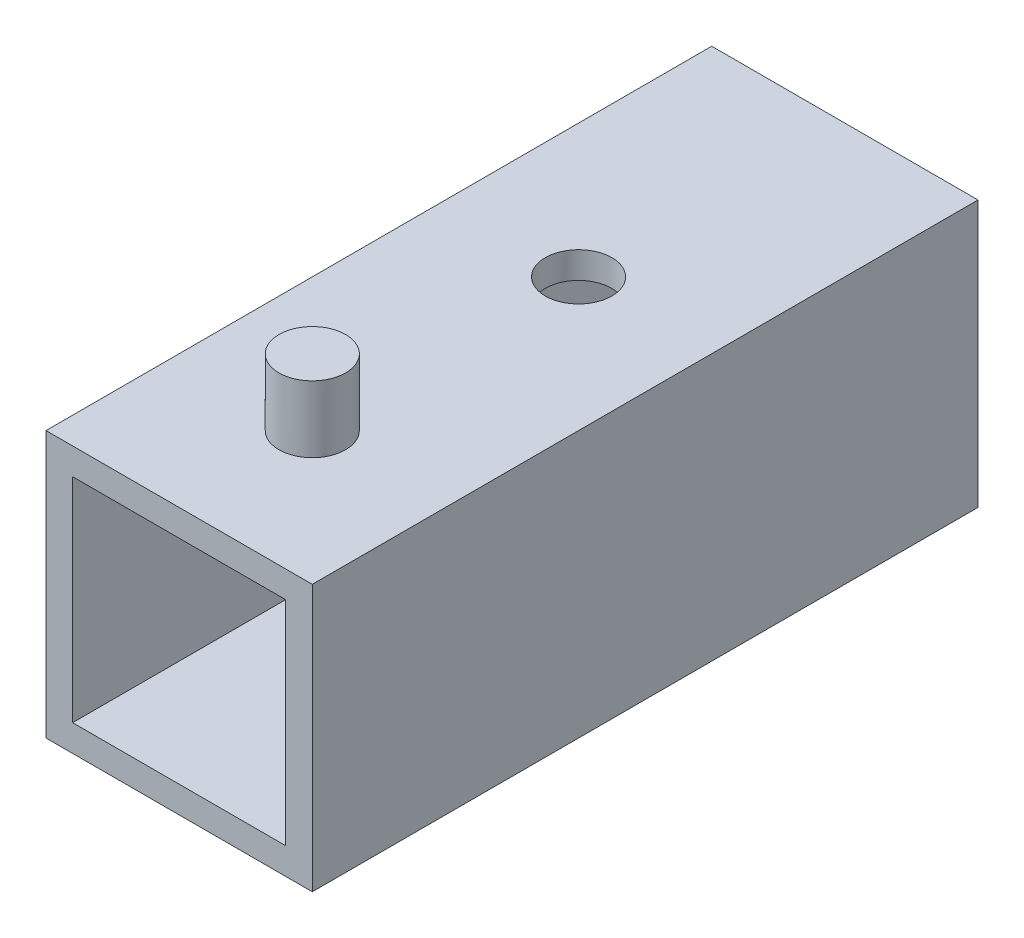
SolidWorks part; units mm, degrees
material "6061-T6 (SS)"
ref_plane "Front Plane" through (0, 0, 0) normal (0, 0, 1) x (1, 0, 0)
ref_plane "Top Plane" through (0, 0, 0) normal (0, 1, 0) x (1, 0, 0)
ref_plane "Right Plane" through (0, 0, 0) normal (1, 0, 0) x (0, 0, -1)
sketch "Sketch1" plane through (0, 0, 0) normal (0, 0, 1) x (1, 0, 0)
  line L1 (-12.7, -12.7) -> (12.7, -12.7)
  line L2 (-12.7, -12.7) -> (-12.7, 12.7)
  line L3 (-12.7, 12.7) -> (12.7, 12.7)
  line L4 (12.7, -12.7) -> (12.7, 12.7)
  line L5 (-12.7, -12.7) -> (12.7, 12.7) construction
  line L6 (-12.7, 12.7) -> (12.7, -12.7) construction
  point P0 (0, 0)
  dimension "D1" = 25.4
  dimension "D2" = 25.4
extrude "Extrude-Thin1" add sketch "Sketch1" along normal mid plane 63.5 thin thin type one direction reverse wall 2.54
sketch "Sketch2" plane through (0, 12.7, 0) normal (0, 1, 0) x (1, 0, 0)
  line L0 (12.7, -31.75) -> (-12.7, -31.75) construction
  circle A0 centre (0, -19.05) radius 3.175
  dimension "D1" = 6.35
  dimension "D2" = 12.7
extrude "Boss-Extrude1" add sketch "Sketch2" along normal blind 6.35 contours A0
sketch "Sketch4" plane through (0, 12.7, 0) normal (0, 1, 0) x (1, 0, 0)
  line L0 (12.7, -31.75) -> (-12.7, -31.75) construction
  circle A0 centre (0, 6.35) radius 3.175
  dimension "D1" = 6.35
  dimension "D2" = 38.1
extrude "Cut-Extrude1" cut sketch "Sketch4" against normal through all
